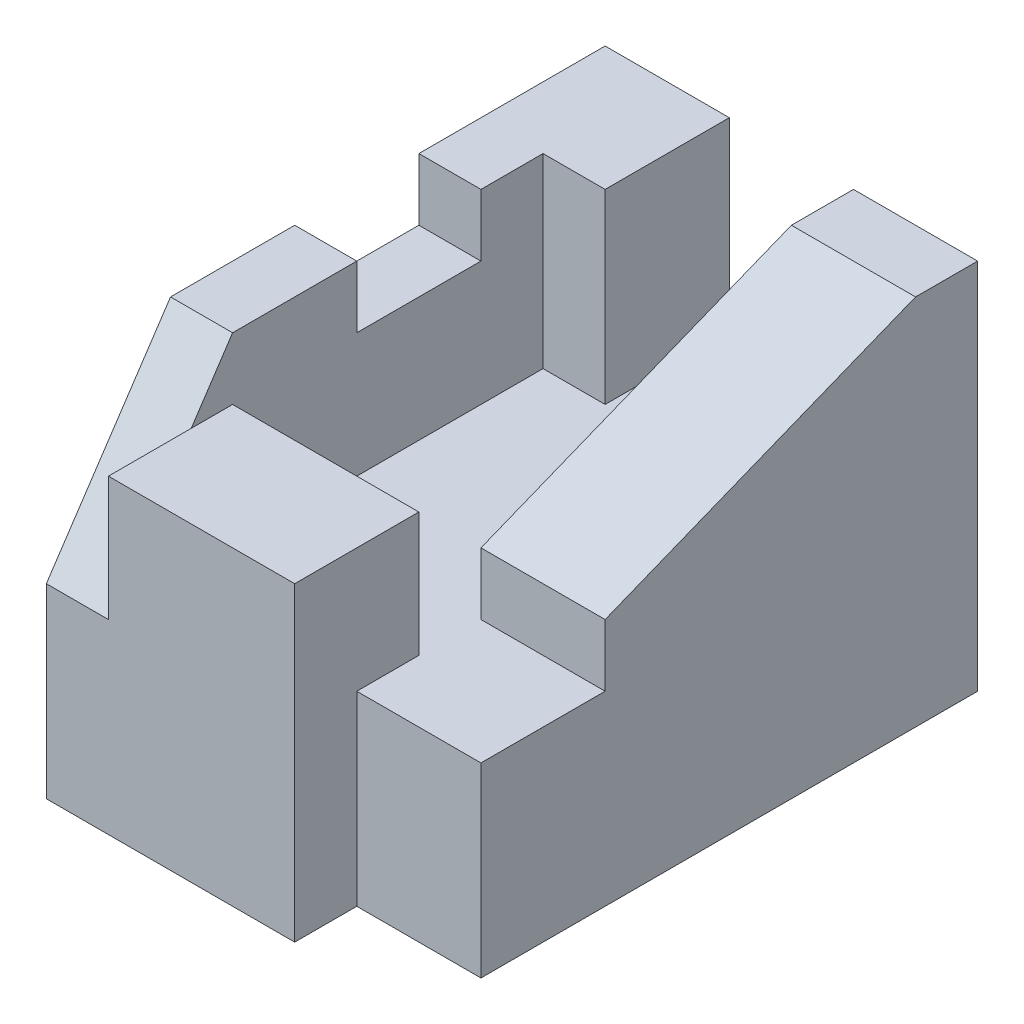
SolidWorks part; units mm, degrees
ref_plane "Front Plane" through (0, 0, 0) normal (0, 0, 1) x (1, 0, 0)
ref_plane "Top Plane" through (0, 0, 0) normal (0, 1, 0) x (1, 0, 0)
ref_plane "Right Plane" through (0, 0, 0) normal (1, 0, 0) x (0, 0, -1)
sketch "Sketch1" plane through (0, 0, 0) normal (0, 0, 1) x (1, 0, 0)
  line L1 (3, -3) -> (-3, -3)
  line L2 (3, -3) -> (3, 3)
  line L3 (3, 3) -> (-3, 3)
  line L4 (-3, -3) -> (-3, 3)
  line L5 (3, -3) -> (-3, 3) construction
  line L6 (3, 3) -> (-3, -3) construction
  point P0 (0, 0)
  dimension "D1" = 6
  dimension "D2" = 6
extrude "Boss-Extrude1" add sketch "Sketch1" along normal blind 9
sketch "Sketch2" plane through (0, 3, 0) normal (0, 1, 0) x (1, 0, 0)
  line L0 (1, 0) -> (-1, 0)
  line L1 (3, 0) -> (-3, 0) construction
  line L2 (-1, 0) -> (-1, -2)
  line L3 (-1, -2) -> (-2, -2)
  line L4 (-2, -2) -> (-2, -7)
  line L5 (-2, -7) -> (1, -7)
  line L6 (1, -7) -> (1, -9)
  line L7 (3, -9) -> (-3, -9) construction
  line L8 (1, -9) -> (3, -9)
  line L9 (3, -9) -> (3, -6)
  line L10 (3, -9) -> (3, 0) construction
  line L11 (3, -6) -> (1, -6)
  line L12 (1, -6) -> (1, 0)
  line L13 (-3, -9) -> (-3, 0) construction
  dimension "D1" = 2
  dimension "D2" = 2
  dimension "D3" = 1
  dimension "D4" = 2
  dimension "D5" = 3
  dimension "D6" = 5
  dimension "D7" = 2
extrude "Cut-Extrude1" cut sketch "Sketch2" against normal blind 3
sketch "Sketch3" plane through (0, 3, 0) normal (0, 1, 0) x (1, 0, 0)
  line L0 (-2, -3) -> (-3, -3)
  line L1 (-2, -2) -> (-2, -7) construction
  line L2 (-3, -9) -> (-3, 0) construction
  line L3 (-3, -3) -> (-3, -5)
  line L4 (-3, -5) -> (-2, -5)
  line L5 (-2, -2) -> (-2, -7) construction
  line L6 (-2, -5) -> (-2, -3)
  line L7 (-1, 0) -> (-3, 0) construction
  dimension "D1" = 3
  dimension "D2" = 2
extrude "Cut-Extrude2" cut sketch "Sketch3" against normal blind 1
sketch "Sketch4" plane through (-3, 0, 0) normal (-1, 0, 0) x (0, 0, 1)
  line L0 (7, 3) -> (9, 0)
  line L1 (9, 3) -> (5, 3) construction
  line L2 (9, 3) -> (9, -3) construction
  line L3 (9, 0) -> (9, 3)
  line L4 (9, 3) -> (7, 3)
  dimension "D1" = 2
  dimension "D2" = 3
extrude "Cut-Extrude3" cut sketch "Sketch4" against normal blind 1
sketch "Sketch5" plane through (1, 0, 0) normal (1, 0, 0) x (0, 0, -1)
  line L0 (-7, 3) -> (-7, 2)
  line L1 (-7, 0) -> (-7, 3) construction
  line L2 (-7, 2) -> (-9, 2)
  line L3 (-9, 0) -> (-9, 3) construction
  line L4 (-9, 2) -> (-9, 3)
  line L5 (-9, 3) -> (-7, 3)
  dimension "D1" = 1
extrude "Cut-Extrude4" cut sketch "Sketch5" against normal blind 3
sketch "Sketch6" plane through (3, 0, 0) normal (1, 0, 0) x (0, 0, -1)
  line L0 (-9, -3) -> (-8, -3)
  line L1 (-9, -3) -> (0, -3) construction
  line L2 (-8, -3) -> (-8, 0)
  line L3 (-7, 0) -> (-9, 0) construction
  line L4 (-8, 0) -> (-9, 0)
  line L5 (-9, 0) -> (-9, -3)
  dimension "D1" = 1
extrude "Cut-Extrude5" cut sketch "Sketch6" against normal blind 2
sketch "Sketch7" plane through (3, 0, 0) normal (1, 0, 0) x (0, 0, -1)
  line L0 (-1, 3) -> (-6, 1)
  line L1 (-6, 3) -> (0, 3) construction
  line L2 (-6, 0) -> (-6, 3) construction
  line L3 (-6, 1) -> (-6, 3)
  line L4 (-6, 3) -> (-1, 3)
  dimension "D1" = 1
  dimension "D2" = 1
extrude "Cut-Extrude6" cut sketch "Sketch7" against normal blind 2
